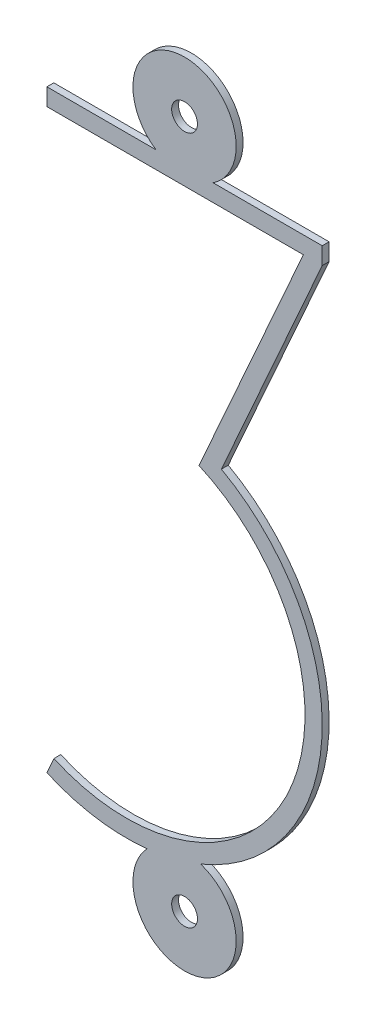
SolidWorks part; units mm, degrees
material "3.0517 (EN-AW 3003)"
ref_plane "Front Plane" through (0, 0, 0) normal (0, 0, 1) x (1, 0, 0)
ref_plane "Top Plane" through (0, 0, 0) normal (0, 1, 0) x (1, 0, 0)
ref_plane "Right Plane" through (0, 0, 0) normal (1, 0, 0) x (0, 0, -1)
sketch "Sketch1" plane through (0, 0, 0) normal (0, 0, 1) x (1, 0, 0)
  line L0 (0, 10) -> (0, -10) construction
  line L1 (-4, 8.75) -> (-0.8292, 8.75)
  line L2 (-4, 8.75) -> (-4, 8.25)
  line L3 (-4, 8.25) -> (3.4528, 8.25)
  line L4 (4, 8.75) -> (4, 8.25)
  line L5 (4, 8.25) -> (1.0708, 1.6631)
  line L6 (3.4528, 8.25) -> (0.4197, 1.4295)
  line L7 (3.5431, 8.4532) -> (0.4197, 1.4295) construction
  line L8 (4, 8.25) -> (0.8766, 1.2263) construction
  line L9 (-4, -9) -> (4, -9) construction
  line L10 (4, -9) -> (4, -3.3114) construction
  line L11 (-4, -9) -> (-4, -8.5092) construction
  line L12 (0.8292, 8.75) -> (4, 8.75)
  line L13 (-4, -8.5092) -> (-3.7968, -8.0524)
  circle A0 centre (0, 10) radius 0.375
  arc A1 (0.8292, 8.75) -> (-0.8292, 8.75) centre (0, 10) ccw
  circle A2 centre (0, -10) radius 0.375
  arc A3 (-1.0889, -8.9683) -> (0.4687, -8.5751) centre (0, -10) ccw
  arc A4 (0.4687, -8.5751) -> (1.0708, 1.6631) centre (-1.6886, -3.3114) ccw
  arc A5 (-3.7968, -8.0524) -> (0.4197, 1.4295) centre (-1.6886, -3.3114) ccw
  arc A7 (-4, -8.5092) -> (-1.0889, -8.9683) centre (-1.6886, -3.3114) ccw
  point P4 (0, -9)
  dimension "D2" = 0.75
  dimension "D3" = 3
  dimension "D4" = 8
  dimension "D10" = 0.5
  dimension "D1" = 20
  dimension "D5" = 1.25
  dimension "D6" = 0.5
  dimension "D7" = 0.5
  dimension "D8" = 1
  dimension "D9" = 8
extrude "Boss-Extrude1" add sketch "Sketch1" along normal mid plane 0.2
sketch "Sketch2" plane through (0, 0, 0) normal (0, 0, 1) x (1, 0, 0)
  line L16 (-4.25, 9) -> (-4.25, 8)
  line L17 (-4.25, 8) -> (3.068, 8)
  line L18 (3.068, 8) -> (0.0871, 1.2968)
  line L19 (-3.9211, -7.7166) -> (-4.3279, -8.6313)
  line L20 (1.3904, 1.7666) -> (4.25, 8.1969)
  line L21 (4.25, 8.1969) -> (4.25, 9)
  line L22 (4.25, 9) -> (1.4361, 9)
  line L23 (-1.4361, 9) -> (-4.25, 9)
  line L24 (-4.25, 9) -> (-4.25, 8)
  line L25 (-4.25, 8) -> (3.068, 8)
  line L26 (3.068, 8) -> (0.0871, 1.2968)
  line L27 (-3.9211, -7.7166) -> (-4.3279, -8.6313)
  line L28 (1.3904, 1.7666) -> (4.25, 8.1969)
  line L29 (4.25, 8.1969) -> (4.25, 9)
  line L30 (4.25, 9) -> (0, 9)
  line L31 (0, 9) -> (-4.25, 9)
  arc A10 (-3.9211, -7.7166) -> (0.0871, 1.2968) centre (-1.6886, -3.3114) ccw
  arc A11 (-4.3279, -8.6313) -> (-1.5807, -9.249) centre (-1.6886, -3.3114) ccw
  arc A12 (-1.5807, -9.249) -> (1.0348, -8.5887) centre (0, -10) ccw
  arc A13 (1.0348, -8.5887) -> (1.3904, 1.7666) centre (-1.6886, -3.3114) ccw
  arc A14 (1.4361, 9) -> (-1.4361, 9) centre (0, 10) ccw
  arc A15 (-3.9211, -7.7166) -> (0.0871, 1.2968) centre (-1.6886, -3.3114) ccw
  arc A16 (-4.3279, -8.6313) -> (-0.0038, -9.006) centre (-1.6886, -3.3114) ccw
  arc A18 (-0.0038, -9.006) -> (1.3904, 1.7666) centre (-1.6886, -3.3114) ccw
  dimension "D1" = 0.25
extrude "Boss-Extrude2" [suppressed] add sketch "Sketch2" along normal mid plane 0.6
